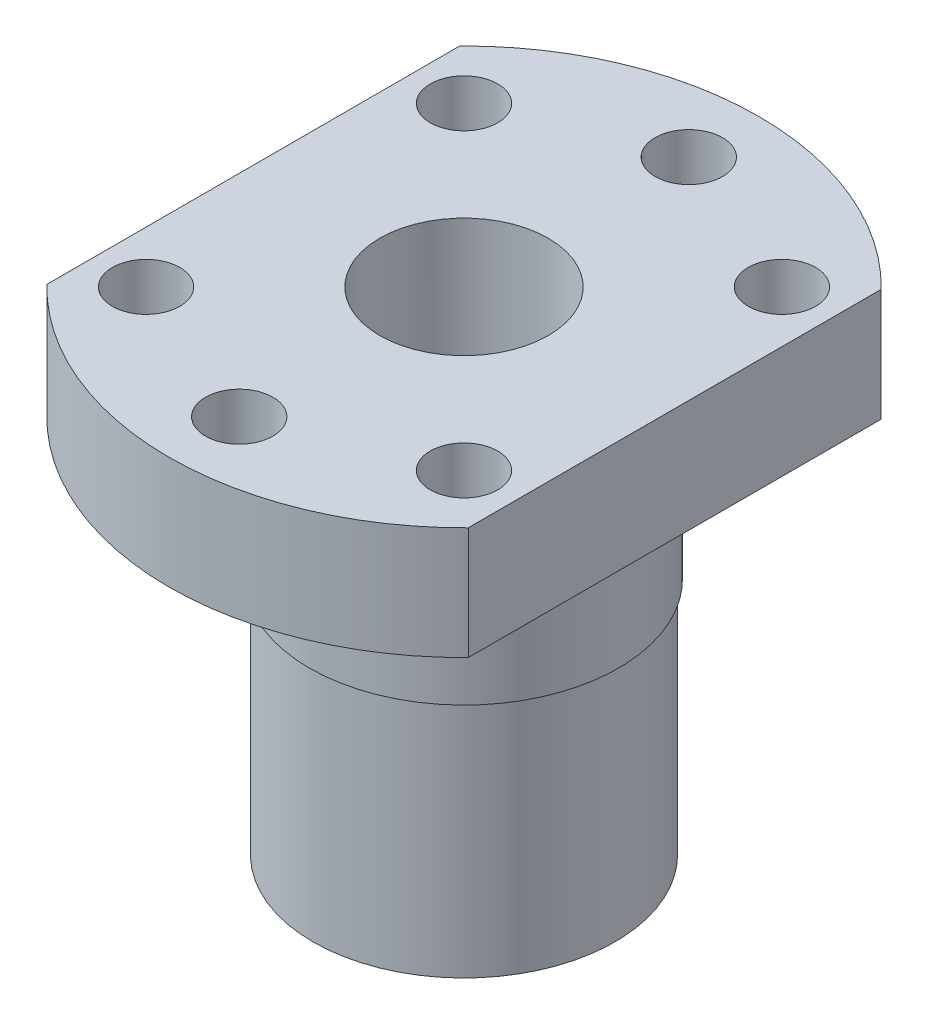
SolidWorks part; units mm, degrees
ref_plane "Front Plane" through (0, 0, 0) normal (0, 0, 1) x (1, 0, 0)
ref_plane "Top Plane" through (0, 0, 0) normal (0, 1, 0) x (1, 0, 0)
ref_plane "Right Plane" through (0, 0, 0) normal (1, 0, 0) x (0, 0, -1)
sketch "Sketch1" plane through (0, 0, 0) normal (0, 1, 0) x (1, 0, 0)
  line L0 (0, 21) -> (0, -21) construction
  line L1 (-11.3137, 11.3137) -> (0, 0) construction
  line L2 (-16, 0) -> (16, 0) construction
  line L3 (-15, 14.6969) -> (-15, -14.6969)
  line L4 (15, 14.6969) -> (15, -14.6969)
  arc A0 (-15, -14.6969) -> (15, -14.6969) centre (0, 0) ccw
  circle A1 centre (0, 0) radius 6
  circle A2 centre (0, 0) radius 16 construction
  circle A3 centre (0, 16) radius 2.4
  arc A4 (15, 14.6969) -> (-15, 14.6969) centre (0, 0) ccw
  circle A5 centre (11.3137, 11.3137) radius 2.4
  circle A6 centre (-11.3137, 11.3137) radius 2.4
  circle A7 centre (11.3137, -11.3137) radius 2.4
  circle A8 centre (0, -16) radius 2.4
  circle A9 centre (-11.3137, -11.3137) radius 2.4
  dimension "D1" = 12
  dimension "D2" = 21
  dimension "D3" = 32
  dimension "D4" = 4.8
  dimension "D5" = 45
  dimension "D6" = 30
extrude "Boss-Extrude1" add sketch "Sketch1" along normal blind 8
sketch "Sketch2" plane through (0, 0, 0) normal (0, -1, 0) x (1, 0, 0)
  circle A0 centre (0, 0) radius 11
  circle A1 centre (0, 0) radius 6 construction
  circle A2 centre (0, 0) radius 6
  dimension "D1" = 22
extrude "Boss-Extrude2" add sketch "Sketch2" along normal blind 10
sketch "Sketch3" plane through (0, -10, 0) normal (0, -1, 0) x (1, 0, 0)
  circle A0 centre (0, 0) radius 6 construction
  circle A1 centre (0, 0) radius 6
  circle A2 centre (0, 0) radius 10.75
  dimension "D1" = 21.5
extrude "Boss-Extrude3" add sketch "Sketch3" along normal blind 17
